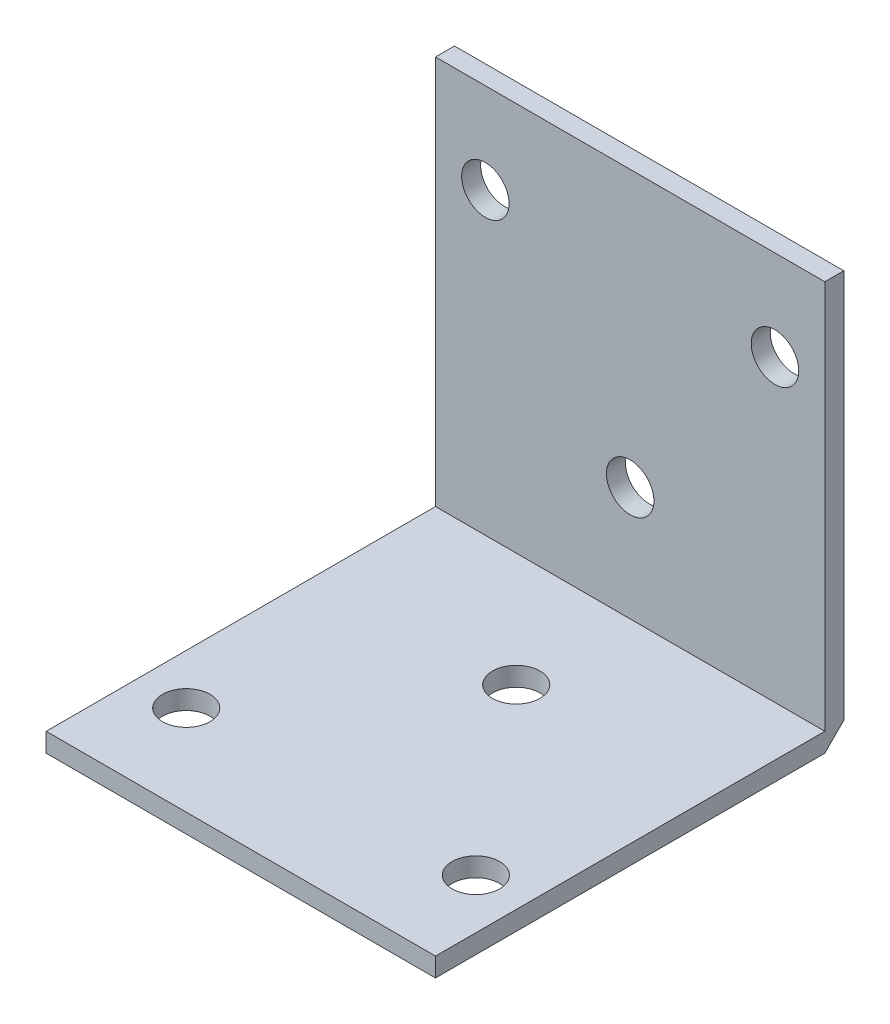
SolidWorks part; units mm, degrees
ref_plane "前视基准面" through (0, 0, 0) normal (0, 0, 1) x (1, 0, 0)
ref_plane "上视基准面" through (0, 0, 0) normal (0, 1, 0) x (1, 0, 0)
ref_plane "右视基准面" through (0, 0, 0) normal (1, 0, 0) x (0, 0, -1)
sketch "草图1" plane through (0, 0, 0) normal (0, 1, 0) x (1, 0, 0)
  line L1 (20.5, -20.5) -> (-20.5, -20.5)
  line L2 (20.5, -20.5) -> (20.5, 20.5)
  line L3 (20.5, 20.5) -> (-20.5, 20.5)
  line L4 (-20.5, -20.5) -> (-20.5, 20.5)
  line L5 (20.5, -20.5) -> (-20.5, 20.5) construction
  line L6 (20.5, 20.5) -> (-20.5, -20.5) construction
  circle A0 centre (-15.25, -11) radius 2.5
  circle A1 centre (15.25, -11) radius 2.5
  circle A2 centre (0, 8.5) radius 2.5
  point P0 (0, 0)
  dimension "D3" = 5
  dimension "D4" = 5
  dimension "D5" = 5
  dimension "D6" = 19.5
  dimension "D7" = 15.25
  dimension "D8" = 12
  dimension "D9" = 19.5
  dimension "D10" = 30.5
  dimension "D1" = 41
  dimension "D2" = 41
extrude "凸台-拉伸1" add sketch "草图1" along normal blind 2
sketch "草图2" plane through (-20.5, 0, 0) normal (-1, 0, 0) x (0, 0, 1)
  line L0 (-22.5, 2) -> (-20.5, 0)
  line L2 (-20.5, 2) -> (-20.5, 43)
  line L3 (-20.5, 43) -> (-22.5, 43)
  line L4 (-22.5, 2) -> (-22.5, 43)
  line L5 (-20.5, 0) -> (-20.5, 2)
  dimension "D1" = 2
  dimension "D2" = 41
extrude "凸台-拉伸2" add sketch "草图2" against normal blind 41
sketch "草图3" plane through (0, 0, -20.5) normal (0, 0, 1) x (1, 0, 0)
  line L0 (-20.5, 2) -> (20.5, 2) construction
  circle A0 centre (-15.25, 33.5) radius 2.5
  circle A1 centre (15.25, 33.5) radius 2.5
  circle A2 centre (0, 14) radius 2.5
  dimension "D1" = 5
  dimension "D2" = 5
  dimension "D3" = 5
  dimension "D4" = 12
  dimension "D5" = 19.5
  dimension "D6" = 19.5
  dimension "D7" = 30.5
  dimension "D8" = 15.25
extrude "切除-拉伸1" cut sketch "草图3" against normal through all
